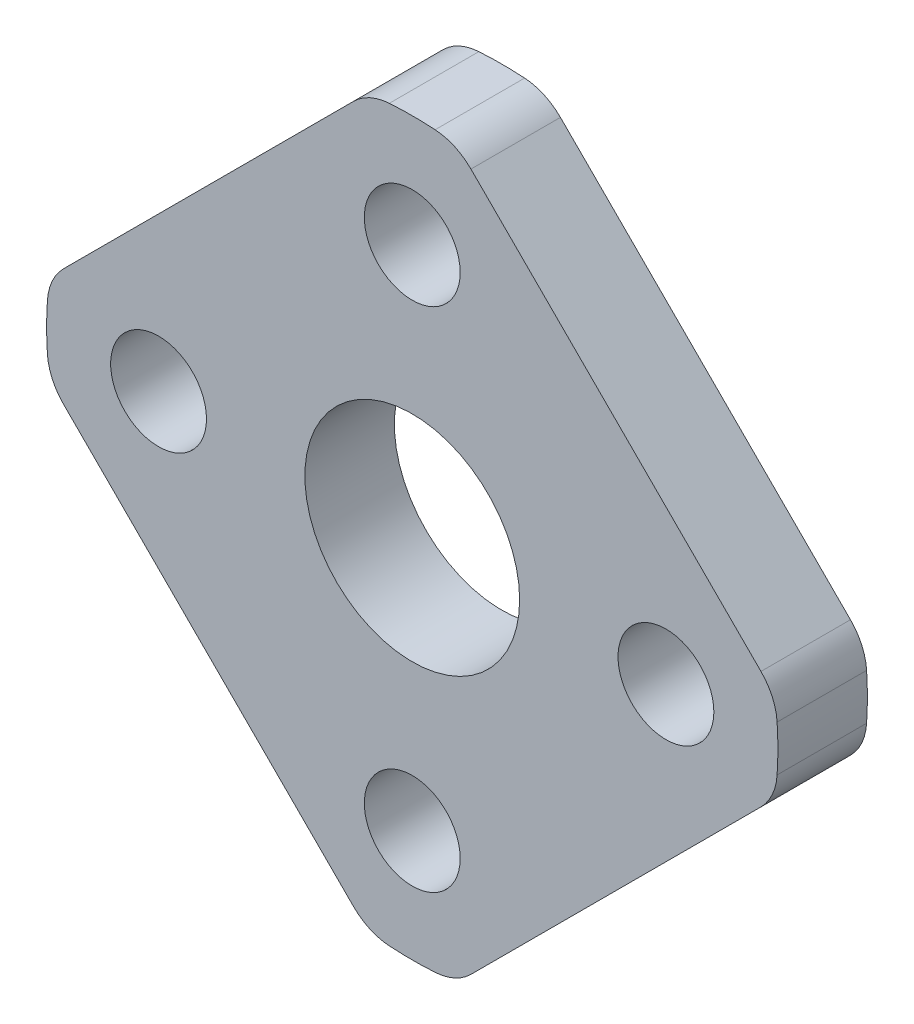
SolidWorks part; units mm, degrees
material "Nylon 101"
ref_plane "Front Plane" through (0, 0, 0) normal (0, 0, 1) x (1, 0, 0)
ref_plane "Top Plane" through (0, 0, 0) normal (0, 1, 0) x (1, 0, 0)
ref_plane "Right Plane" through (0, 0, 0) normal (1, 0, 0) x (0, 0, -1)
sketch "Sketch1" plane through (0, 0, 0) normal (0, 0, 1) x (1, 0, 0)
  line L5 (-2.0819, 12.3714) -> (-12.3714, 2.0819)
  line L6 (-12.3714, -2.0819) -> (-2.0819, -12.3714)
  line L10 (2.0819, -12.3714) -> (12.3714, -2.0819)
  line L11 (12.3714, 2.0819) -> (2.0819, 12.3714)
  circle A0 centre (0, -9) radius 1.7
  circle A1 centre (-9, 0) radius 1.7
  circle A2 centre (0, 9) radius 1.7
  circle A3 centre (9, 0) radius 1.7
  circle A16 centre (0, 0) radius 3.81
  arc A17 (-12.3714, 2.0819) -> (-12.9445, 0.8122) centre (-10.9784, 0.6889) ccw
  arc A18 (-12.9445, 0.8122) -> (-12.9445, -0.8122) centre (0, 0) ccw
  arc A19 (-12.9445, -0.8122) -> (-12.3714, -2.0819) centre (-10.9784, -0.6889) ccw
  arc A20 (-2.0819, -12.3714) -> (-0.8122, -12.9445) centre (-0.6889, -10.9784) ccw
  arc A21 (-0.8122, -12.9445) -> (0.8122, -12.9445) centre (0, 0) ccw
  arc A22 (0.8122, -12.9445) -> (2.0819, -12.3714) centre (0.6889, -10.9784) ccw
  arc A23 (12.3714, -2.0819) -> (12.9445, -0.8122) centre (10.9784, -0.6889) ccw
  arc A24 (12.9445, -0.8122) -> (12.9445, 0.8122) centre (0, 0) ccw
  arc A25 (12.9445, 0.8122) -> (12.3714, 2.0819) centre (10.9784, 0.6889) ccw
  arc A26 (2.0819, 12.3714) -> (0.8122, 12.9445) centre (0.6889, 10.9784) ccw
  arc A27 (0.8122, 12.9445) -> (-0.8122, 12.9445) centre (0, 0) ccw
  arc A28 (-0.8122, 12.9445) -> (-2.0819, 12.3714) centre (-0.6889, 10.9784) ccw
  point P0 (0, 0)
  dimension "D3" = 3.4
  dimension "D6" = 7.62
extrude "Boss-Extrude1" add sketch "Sketch1" along normal blind 3.175
